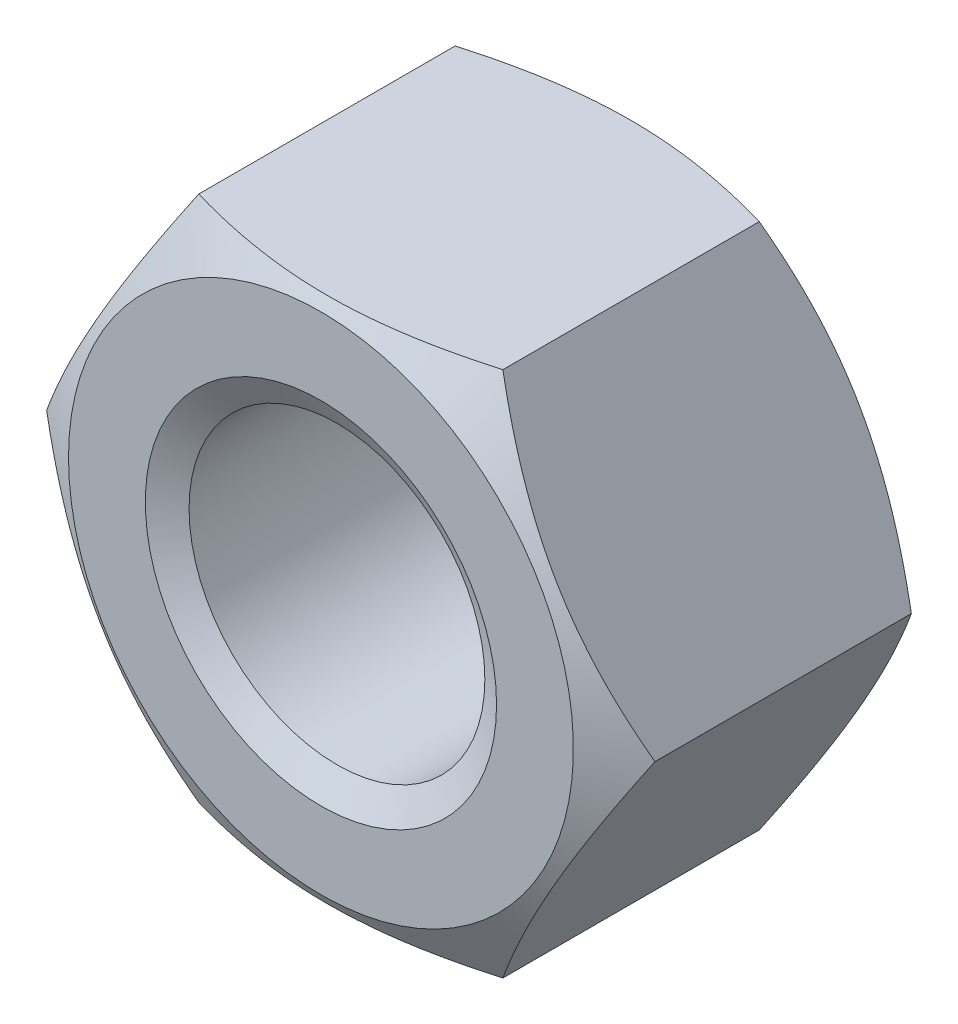
SolidWorks part; units mm, degrees
ref_plane "Front" through (0, 0, 0) normal (0, 0, 1) x (1, 0, 0)
ref_plane "Top" through (0, 0, 0) normal (0, 1, 0) x (1, 0, 0)
ref_plane "Right" through (0, 0, 0) normal (1, 0, 0) x (0, 0, -1)
sketch "Sketch1" plane through (0, 0, 0) normal (0, 0, 1) x (1, 0, 0)
  line L1 (10.3923, 0) -> (5.1962, 9)
  line L2 (5.1962, 9) -> (-5.1962, 9)
  line L3 (-5.1962, 9) -> (-10.3923, 0)
  line L4 (-10.3923, 0) -> (-5.1962, -9)
  line L5 (-5.1962, -9) -> (5.1962, -9)
  line L6 (5.1962, -9) -> (10.3923, 0)
  circle A0 centre (0, 0) radius 9 construction
  circle A1 centre (0, 0) radius 5.053
  dimension "D" = 10.106
  dimension "s" = 18
extrude "BaseNut" add sketch "Sketch1" against normal blind 10.8
cosmetic thread "ThreadCosmetic1" parameters "D"=12
sketch "Sketch2" plane through (0, 0, 0) normal (0, 1, 0) x (1, 0, 0)
  line L0 (-10.3923, 10.8) -> (-8.625, 10.8)
  line L2 (-8.625, 10.8) -> (-10.3923, 9.7796)
  line L3 (-10.3923, 9.7796) -> (-10.3923, 10.8)
  line L4 (0, 3.3759) -> (0, -9.8171) construction
  line L6 (-9.7712, 5.4) -> (9.8853, 5.4) construction
  line L7 (-10.3923, 1.0204) -> (-10.3923, 0)
  line L8 (-8.625, 0) -> (-10.3923, 1.0204)
  line L9 (-10.3923, 0) -> (-8.625, 0)
  dimension "D1" = 30
  dimension "dw" = 17.25
  dimension "D2" = 5.4
revolve "Double-Chamfer" cut sketch "Sketch2" angle 360 about L4
chamfer "EndChamfer" distance 0.947 angle 30 2 edges at (5.053, 0, -10.8) (5.053, 0, 0)
sketch "Sketch3" plane through (0, 0, 0) normal (0, 1, 0) x (1, 0, 0)
  line L0 (-5.8731, 9.853) -> (-5.053, 9.3795)
  line L1 (-5.053, 9.3795) -> (-4.106, 9.3795)
  line L2 (-4.106, 9.3795) -> (-4.106, 10.3265)
  line L3 (-4.106, 10.3265) -> (-5.053, 10.3265)
  line L4 (-5.053, 10.3265) -> (-5.8731, 9.853)
  line L5 (0, 7.4383) -> (0, 16.8806) construction
  dimension "D1" = 0.947
  dimension "D2" = 10.106
revolve "Cut-Revolve10" [suppressed] cut sketch "Sketch3" angle 360 about L5
pattern_linear "LPattern10" [suppressed] count 10 spacing 1.1364 along (0, 0, -1)
equation "\"dw@Sketch2\" = \"s@Sketch1\"-0.75"
equation "\"D2@Sketch2\" = \"m@BaseNut\" / 2"
equation "\"D2@Sketch3\" = \"D@Sketch1\""
equation "\"D1@Sketch3\" =  (\"D@ThreadCosmetic1\"   - \"D@Sketch1\")  / 2"
equation "\"D3@LPattern10\" = \"D1@Sketch3\" * 1.2"
equation "\"D1@LPattern10\" = \"m@BaseNut\"/\"D3@LPattern10\""
